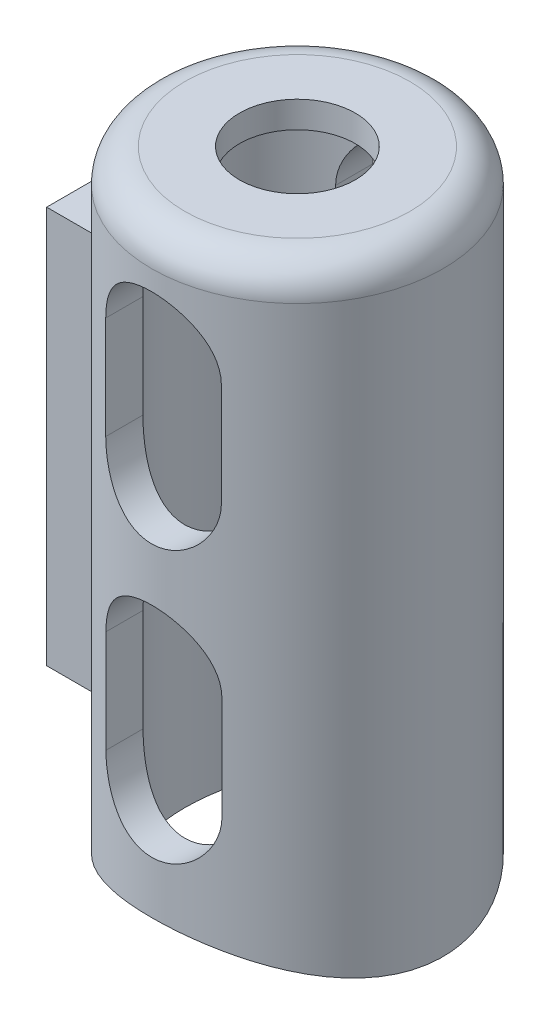
SolidWorks part; units mm, degrees
material "ABS"
ref_plane "Front Plane" through (0, 0, 0) normal (0, 0, 1) x (1, 0, 0)
ref_plane "Top Plane" through (0, 0, 0) normal (0, 1, 0) x (1, 0, 0)
ref_plane "Right Plane" through (0, 0, 0) normal (1, 0, 0) x (0, 0, -1)
sketch "Sketch1" plane through (0, 0, 0) normal (0, 1, 0) x (1, 0, 0)
  circle A0 centre (0, 0) radius 11.176
  circle A1 centre (0, 0) radius 8.636
  dimension "D1" = 22.352
  dimension "D2" = 17.272
extrude "Boss-Extrude1" add sketch "Sketch1" along normal blind 45.72 and the other way blind 2.54
sketch "Sketch2" plane through (0, 45.72, 0) normal (0, 1, 0) x (1, 0, 0)
  circle A0 centre (0, 0) radius 10.668
extrude "Boss-Extrude2" add sketch "Sketch2" against normal blind 2.032
sketch "Sketch3" plane through (0, 0, 0) normal (0, 0, 1) x (1, 0, 0)
  line L0 (55, 0) -> (-55, 0) construction
  line L1 (-0.0152, 24.8919) -> (0.0152, 20.8281) construction
  line L4 (0, 45.72) -> (0, 0) construction
  line L6 (-0.0152, 37.211) -> (-0.0152, 29.3369) construction
  line L7 (4.4298, 37.211) -> (4.4298, 29.3369)
  line L8 (-4.4602, 37.211) -> (-4.4602, 29.3369)
  line L9 (0.0152, 8.509) -> (0.0152, 16.3831) construction
  line L10 (-4.4298, 8.509) -> (-4.4298, 16.3831)
  line L11 (4.4602, 8.509) -> (4.4602, 16.3831)
  line L12 (11.176, 45.72) -> (-11.176, 45.72) construction
  arc A2 (4.4298, 37.211) -> (-4.4602, 37.211) centre (-0.0152, 37.211) ccw
  arc A3 (-4.4602, 29.3369) -> (4.4298, 29.3369) centre (-0.0152, 29.3369) ccw
  arc A4 (-4.4298, 8.509) -> (4.4602, 8.509) centre (0.0152, 8.509) ccw
  arc A5 (4.4602, 16.3831) -> (-4.4298, 16.3831) centre (0.0152, 16.3831) ccw
  point P0 (0.0152, 4.064)
  point P6 (-0.0152, 41.656)
  point P7 (-0.0152, 24.8919)
  point P8 (0.0152, 20.8281)
  point P12 (0, 22.86)
  point P13 (0, 22.86)
  point P18 (-0.0152, 33.274)
  point P25 (0.0152, 12.446)
  dimension "D2" = 4.064
  dimension "D3" = 4.064
  dimension "D4" = 8.89
  dimension "D1" = 4.064
  dimension "D5" = 8.89
extrude "Cut-Extrude1" cut sketch "Sketch3" against normal through all and the other way through all
sketch "Sketch4" plane through (0, 45.72, 0) normal (0, 1, 0) x (1, 0, 0)
  circle A0 centre (0, 0) radius 4.445
  dimension "D1" = 8.89
extrude "Cut-Extrude2" cut sketch "Sketch4" against normal up to next
ref_plane "Plane1" through (-10.668, 0, 0) normal (1, 0, 0) x (0, 0, -1)
sketch "Sketch5" plane through (-10.668, 0, 0) normal (1, 0, 0) x (0, 0, -1)
  line L0 (0, 45.72) -> (0, 0) construction
  line L1 (11.176, 45.72) -> (-11.176, 45.72) construction
  line L2 (0, 22.86) -> (11.176, 0.762) construction
  line L3 (11.176, -2.54) -> (11.176, 4.064) construction
  line L5 (-6.0325, 7.62) -> (6.0325, 7.62)
  line L6 (-6.0325, 7.62) -> (-6.0325, 38.1)
  line L7 (-6.0325, 38.1) -> (6.0325, 38.1)
  line L8 (6.0325, 7.62) -> (6.0325, 38.1)
  line L9 (-6.0325, 7.62) -> (6.0325, 38.1) construction
  line L10 (-6.0325, 38.1) -> (6.0325, 7.62) construction
  dimension "D1" = 30.48
  dimension "D2" = 12.065
extrude "Boss-Extrude3" add sketch "Sketch5" along normal blind 2.032 and the other way blind 2.54
sketch "Sketch6" plane through (-13.208, 0, 0) normal (-1, 0, 0) x (0, 0, 1)
  line L0 (-6.0325, 38.1) -> (6.0325, 7.62) construction
  line L1 (6.0325, 38.1) -> (-6.0325, 7.62) construction
  circle A0 centre (0, 22.86) radius 3.683
  dimension "D1" = 7.366
extrude "Cut-Extrude3" cut sketch "Sketch6" against normal blind 2.286
sketch "Sketch8" plane through (-13.208, 0, 0) normal (-1, 0, 0) x (0, 0, 1)
  line L0 (0, 0) -> (0, -2.5857) construction
  line L2 (-13.8947, -6.7688) -> (13.8947, -6.7688)
  line L3 (-13.8947, -6.7688) -> (-13.8947, 1.5974)
  line L5 (13.8947, -6.7688) -> (13.8947, 1.5974)
  line L6 (-13.8947, -6.7688) -> (13.8947, 1.5974) construction
  line L7 (-13.8947, 1.5974) -> (13.8947, -6.7688) construction
  arc A1 (-13.8947, 1.5974) -> (13.8947, 1.5974) centre (0, 22.86) ccw
  dimension "D2" = 50.8
  dimension "D1" = 2.5857
  dimension "D3" = 8.3662
  dimension "D4" = 27.7894
extrude "Cut-Extrude4" cut sketch "Sketch8" against normal through all
fillet "Fillet1" radius 2.54 1 edges at (0, 45.72, 11.176)
